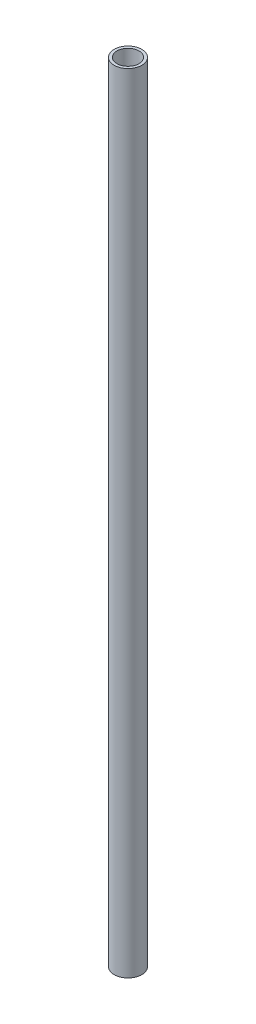
SolidWorks part; units mm, degrees
ref_plane "前视基准面" through (0, 0, 0) normal (0, 0, 1) x (1, 0, 0)
ref_plane "上视基准面" through (0, 0, 0) normal (0, 1, 0) x (1, 0, 0)
ref_plane "右视基准面" through (0, 0, 0) normal (1, 0, 0) x (0, 0, -1)
sketch "草图1" plane through (0, 0, 0) normal (0, 1, 0) x (1, 0, 0)
  circle A0 centre (0, 0) radius 12.5
extrude "凸台-拉伸1" add sketch "草图1" along normal mid plane 712
sketch "草图2" plane through (0, 356, 0) normal (0, 1, 0) x (1, 0, 0)
  circle A0 centre (0, 0) radius 10
extrude "切除-拉伸1" cut sketch "草图2" against normal blind 20
sketch "草图3" plane through (0, 356, 0) normal (0, 1, 0) x (1, 0, 0)
  circle A0 centre (0, 0) radius 3
extrude "切除-拉伸2" cut sketch "草图3" against normal blind 800
sketch "草图4" plane through (0, -356, 0) normal (0, -1, 0) x (1, 0, 0)
  circle A1 centre (0, 0) radius 12
extrude "切除-拉伸3" cut sketch "草图4" against normal blind 20
sketch "草图5" plane through (0, 0, 0) normal (0, 0, 1) x (1, 0, 0)
  line L0 (-12.5, 356) -> (-12.5, 544.5847)
  line L1 (-12.5, 356) -> (12.5, 356)
  line L2 (-12.5, 356) -> (-12.5, -356)
  line L3 (-12.5, -356) -> (12.5, -356)
  line L4 (12.5, 356) -> (12.5, -356)
